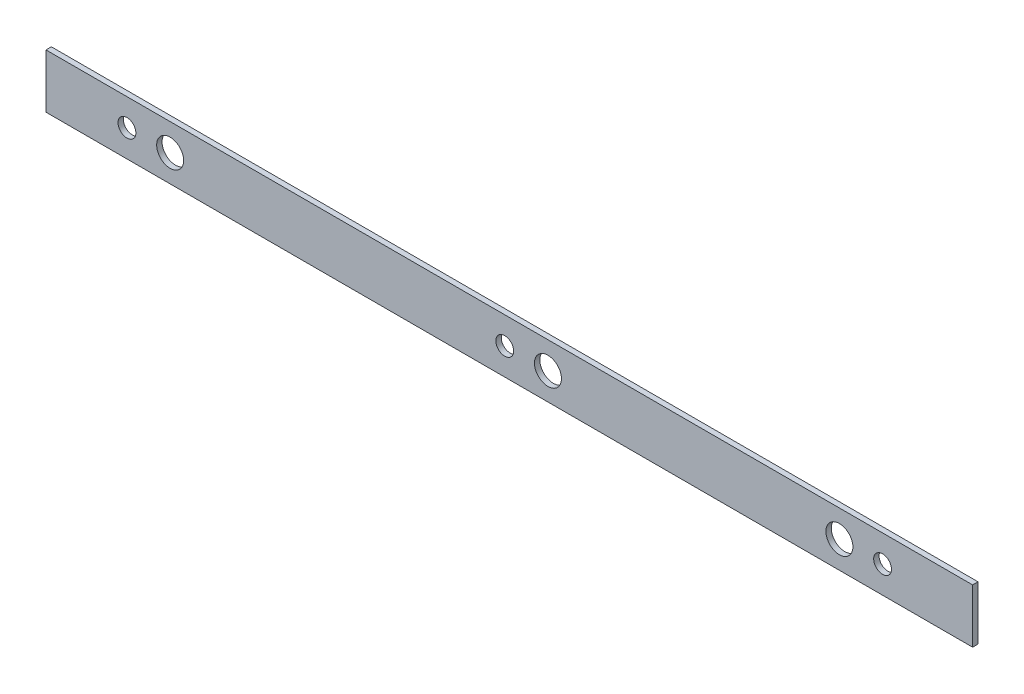
SolidWorks part; units mm, degrees
ref_plane "Front Plane" through (0, 0, 0) normal (0, 0, 1) x (1, 0, 0)
ref_plane "Top Plane" through (0, 0, 0) normal (0, 1, 0) x (1, 0, 0)
ref_plane "Right Plane" through (0, 0, 0) normal (1, 0, 0) x (0, 0, -1)
sketch "Sketch1" plane through (0, 0, 0) normal (0, 0, 1) x (1, 0, 0)
  line L1 (-223.1003, 272.5) -> (-51.4191, 272.5)
  line L2 (-223.1003, 272.5) -> (-223.1003, 262.5)
  line L3 (-223.1003, 262.5) -> (-51.4191, 262.5)
  line L4 (-51.4191, 272.5) -> (-51.4191, 262.5)
  circle A0 centre (-200.1003, 267.5) radius 2.5
  circle A1 centre (-208.1003, 267.5) radius 1.65
  circle A2 centre (-138.1003, 267.5) radius 1.65
  circle A3 centre (-130.1003, 267.5) radius 2.5
  circle A4 centre (-76.1003, 267.5) radius 2.5
  circle A5 centre (-68.1003, 267.5) radius 1.65
extrude "Boss-Extrude1" add sketch "Sketch1" along normal blind 1
